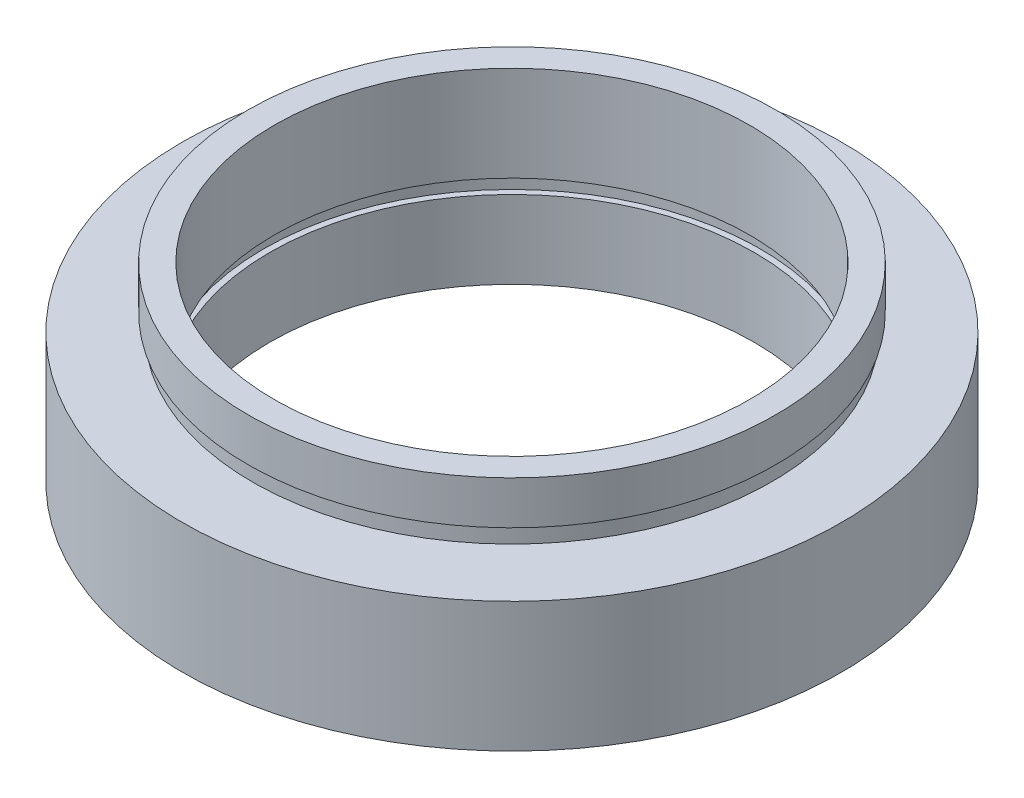
SolidWorks part; units mm, degrees
ref_plane "前视基准面" through (0, 0, 0) normal (0, 0, 1) x (1, 0, 0)
ref_plane "上视基准面" through (0, 0, 0) normal (0, 1, 0) x (1, 0, 0)
ref_plane "右视基准面" through (0, 0, 0) normal (1, 0, 0) x (0, 0, -1)
sketch "草图1" plane through (0, 0, 0) normal (0, 0, 1) x (1, 0, 0)
  line L0 (0, 16.886) -> (0, -24.4878) construction
  line L1 (14, 0) -> (14, 4.5)
  line L2 (13.74, 5.5) -> (14.35, 5.5)
  line L3 (13.74, 5.5) -> (13.74, 11)
  line L4 (13.74, 11) -> (15.26, 11)
  line L5 (15.26, 11) -> (15.26, 8.5)
  line L6 (15.26, 8.5) -> (15, 8.5)
  line L7 (15, 8.5) -> (15, 7.5)
  line L8 (15, 7.5) -> (19.05, 7.5)
  line L9 (19.05, 7.5) -> (19.05, 0)
  line L10 (19.05, 0) -> (14, 0)
  line L11 (14, 4.5) -> (14.35, 4.5)
  line L12 (14.35, 4.5) -> (14.35, 5.5)
  line L13 (0, 0) -> (3.4668, 0) construction
  point P4 (16.525, 0)
  dimension "D1" = 13.74
  dimension "D2" = 15.26
  dimension "D3" = 15
  dimension "D4" = 14
  dimension "D5" = 14.35
  dimension "D6" = 19.05
  dimension "D7" = 11
  dimension "D8" = 7.5
  dimension "D9" = 1
  dimension "D10" = 4.5
  dimension "D11" = 1
revolve "旋转1" add sketch "草图1" angle 360 about L0
cosmetic thread "装饰螺纹线1" parameters "D2"=30.5
cosmetic thread "装饰螺纹线2" parameters "D2"=27.5
cosmetic thread "装饰螺纹线3" parameters "D2"=28.5
